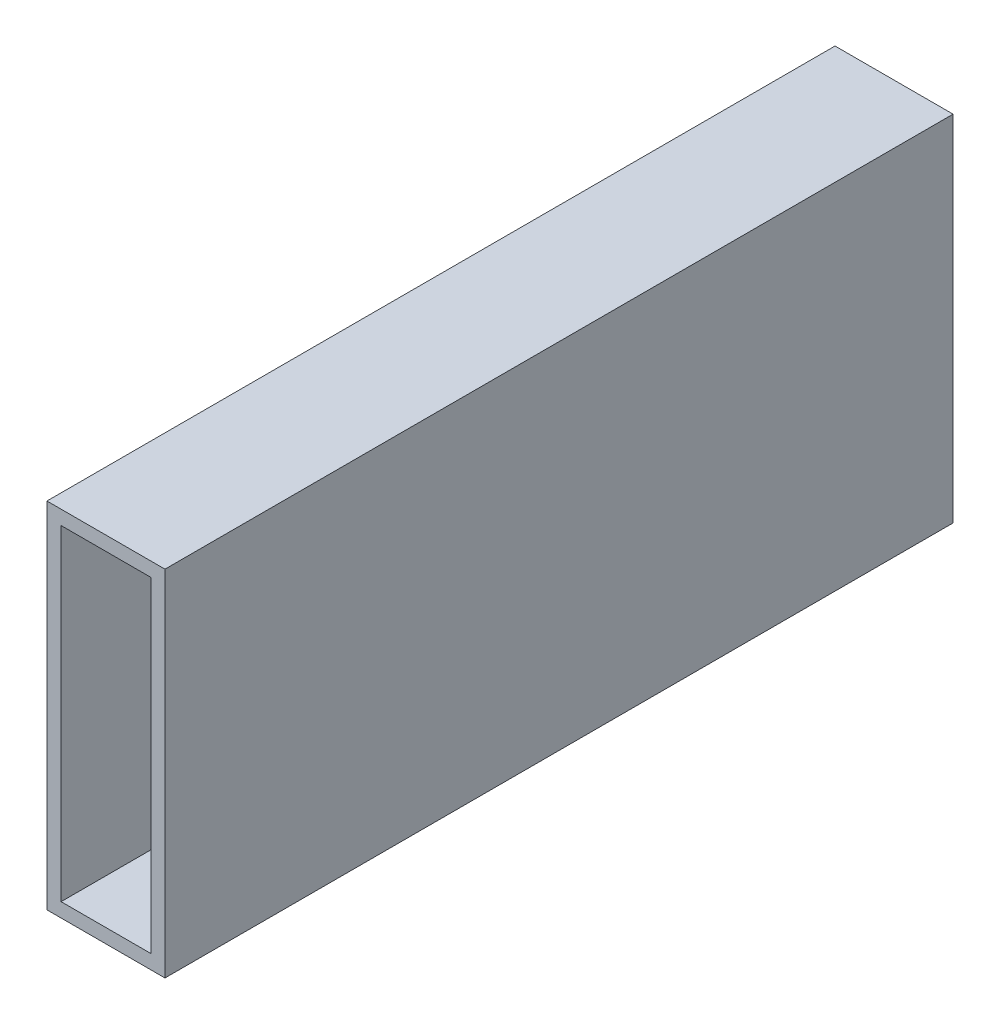
SolidWorks part; units mm, degrees
material "A500"
ref_plane "Front Plane" through (0, 0, 0) normal (0, 0, 1) x (1, 0, 0)
ref_plane "Top Plane" through (0, 0, 0) normal (0, 1, 0) x (1, 0, 0)
ref_plane "Right Plane" through (0, 0, 0) normal (1, 0, 0) x (0, 0, -1)
sketch "Sketch2" plane through (0, 0, 0) normal (0, 0, 1) x (1, 0, 0)
  line L0 (0, 0) -> (0, 38.1)
  line L1 (0, 38.1) -> (12.7, 38.1)
  line L2 (12.7, 38.1) -> (12.7, 0)
  line L3 (12.7, 0) -> (0, 0)
  line L4 (12.7, -38.1) -> (12.7, -35.052)
  line L5 (0, 0) -> (-12.7, 0)
  line L6 (0, 0) -> (0, -38.1)
  line L7 (0, -38.1) -> (-12.7, -38.1)
  line L8 (-12.7, 0) -> (-12.7, -38.1)
  line L9 (-12.7, -38.1) -> (12.7, -38.1)
  line L10 (-12.7, -38.1) -> (-12.7, 38.1)
  line L11 (-12.7, 38.1) -> (12.7, 38.1)
  line L12 (12.7, -38.1) -> (12.7, 38.1)
  line L13 (12.7, -35.052) -> (9.652, -35.052)
  line L14 (-12.7, 38.1) -> (-9.652, 38.1)
  line L15 (-9.652, 38.1) -> (-9.652, 35.052)
  line L17 (-9.652, 35.052) -> (9.652, 35.052)
  line L18 (-9.652, 35.052) -> (-9.652, -35.052)
  line L19 (-9.652, -35.052) -> (9.652, -35.052)
  line L20 (9.652, 35.052) -> (9.652, -35.052)
  dimension "D1" = 38.1
  dimension "D2" = 12.7
  dimension "D3" = 38.1
  dimension "D4" = 12.7
  dimension "D5" = 3.048
  dimension "D6" = 3.048
  dimension "D7" = 3.048
  dimension "D8" = 3.048
extrude "Boss-Extrude1" add sketch "Sketch2" along normal up to vertex (182.3 mm away) contours L18 L15 L11 L10 L5 | L15 L17 L0 L11 | L17 L20 L3 L2 L1 L0 | L3 L20 L13 L12 | L19 L18 L5 L8 L7 L6 | L19 L6 L9 L4 L13
ref_plane "Plane1" through (310, 0, 195) normal (-1, 0, 0) x (0, 0, 1)
sketch "Sketch3" plane through (310, 0, 195) normal (-1, 0, 0) x (0, 0, 1)
  line L0 (12.7, 38.1) -> (-12.7, -38.1)
  line L1 (12.7, -38.1) -> (-12.7, -38.1)
  line L2 (12.7, -38.1) -> (12.7, 38.1)
  line L3 (12.7, 38.1) -> (-12.7, 38.1)
  line L4 (-12.7, -38.1) -> (-12.7, 38.1)
  line L5 (-182.3, 38.1) -> (-207.7, -38.1)
  line L6 (-182.3, 38.1) -> (-207.7, 38.1)
  line L7 (-182.3, 38.1) -> (-182.3, -38.1)
  line L8 (-182.3, -38.1) -> (-207.7, -38.1)
  line L9 (-207.7, 38.1) -> (-207.7, -38.1)
  point P4 (0, 0)
  point P10 (-195, 0)
  dimension "D1" = 25.4
  dimension "D2" = 76.2
  dimension "D3" = 25.4
  dimension "D4" = 76.2
extrude "Cut-Extrude1" cut sketch "Sketch3" against normal through all both and the other way through all contours L4 L0 L3 | L1 L2 L0 | L6 L9 L5 | L8 L7 L5
equation "\"D3@Sketch2\"=\"D1@Sketch2\""
equation "\"D4@Sketch2\"=\"D2@Sketch2\""
